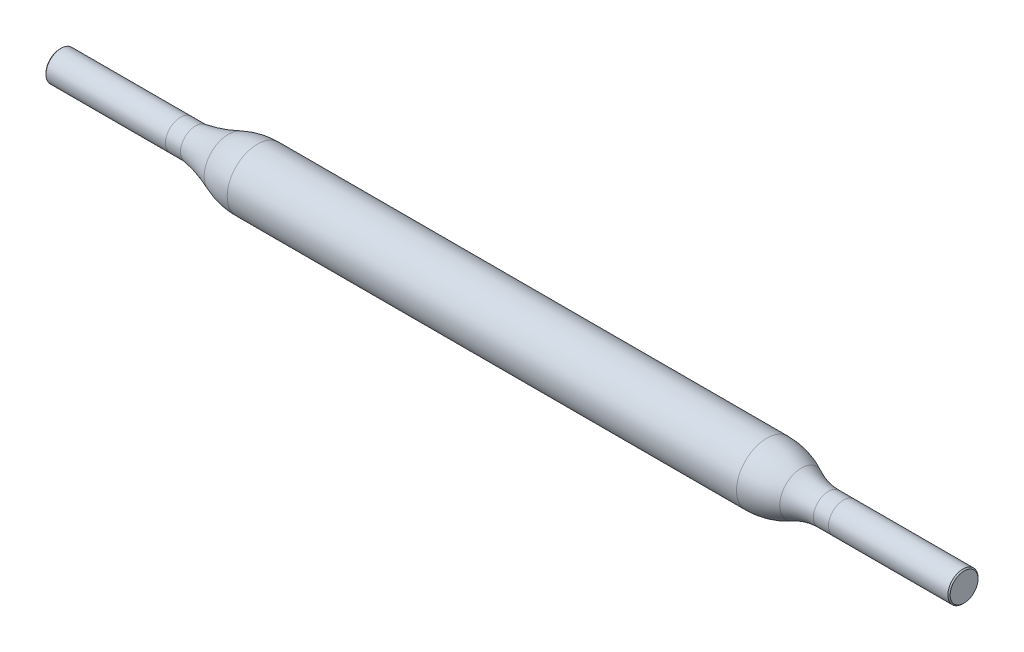
SolidWorks part; units mm, degrees
ref_plane "Front Plane" through (0, 0, 0) normal (0, 0, 1) x (1, 0, 0)
ref_plane "Top Plane" through (0, 0, 0) normal (0, 1, 0) x (1, 0, 0)
ref_plane "Right Plane" through (0, 0, 0) normal (1, 0, 0) x (0, 0, -1)
sketch "Sketch1" plane through (0, 0, 0) normal (0, 0, 1) x (1, 0, 0)
  line L0 (-30, 0) -> (30, 0)
  line L1 (30, 0) -> (30, 1)
  line L2 (-30, 0) -> (-30, 1)
  line L3 (-30, 1) -> (-21, 1)
  line L4 (-16.9, 2) -> (16.9, 2)
  line L5 (30, 1) -> (21, 1)
  arc A0 (-21, 1) -> (-18.8111, 1.6204) centre (-22.5675, 10.7026) ccw
  arc A1 (19.2021, 1.4385) -> (21, 1) centre (21, 4.9048) ccw
  arc A2 (16.9, 2) -> (19.2021, 1.4385) centre (16.9, -3) cw
  arc A3 (-16.9, 2) -> (-18.8111, 1.6204) centre (-16.9, -3) ccw
  point P2 (0, 0)
  point P12 (0, 2)
  point P17 (-18, 2)
  dimension "D8" = 5
  dimension "D1" = 60
  dimension "D2" = 1
  dimension "D3" = 1
  dimension "D4" = 9
  dimension "D5" = 9
  dimension "D6" = 2
  dimension "D7" = 3
revolve "Revolve1" add sketch "Sketch1" angle 360 about L0
sketch "Sketch2" plane through (0, 0, 0) normal (0, 0, 1) x (1, 0, 0)
  line L0 (-22, 7.5989) -> (-22, -8.265)
  line L1 (22, 7.5989) -> (22, -9.2943)
  line L2 (-30, 1) -> (-30, -1) construction
  line L3 (30, -1) -> (30, 1) construction
  dimension "D1" = 8
  dimension "D2" = 8
split line "Split Line1"
chamfer "Chamfer1" distance 0.075 angle 45 2 edges at (30, 0, 1) (-30, 0, 1)
